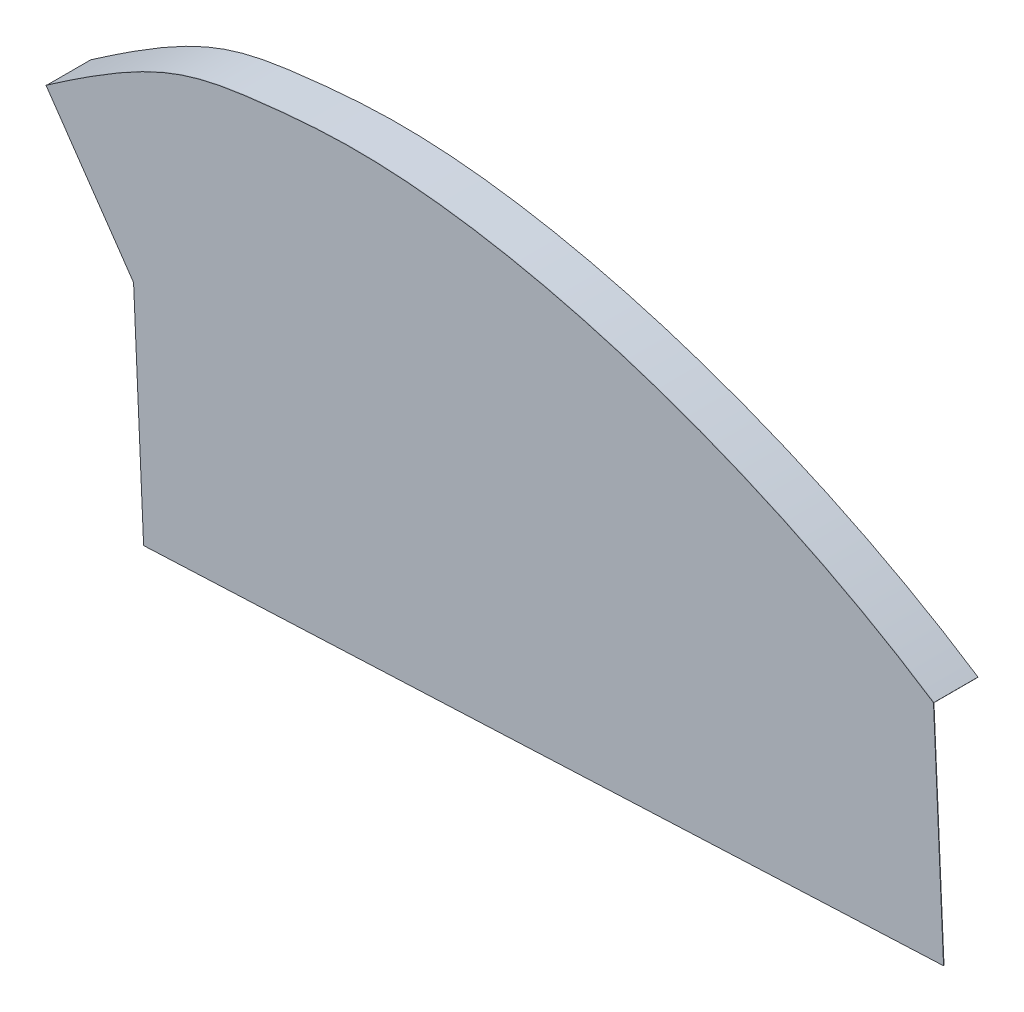
SolidWorks part; units mm, degrees
ref_plane "Front Plane" through (0, 0, 0) normal (0, 0, 1) x (1, 0, 0)
ref_plane "Top Plane" through (0, 0, 0) normal (0, 1, 0) x (1, 0, 0)
ref_plane "Right Plane" through (0, 0, 0) normal (1, 0, 0) x (0, 0, -1)
sketch "Sketch1" plane through (0, 0, 0) normal (0, 0, 1) x (1, 0, 0)
  line L0 (-169.0031, 11.7142) -> (-694.187, 895.1707) construction
  line L1 (-1544.65, 573.4414) -> (-1542.3973, 523.4922)
  line L2 (-1743.608, 593.8305) -> (-1723.9756, 565.3542)
  line L3 (-1544.65, 573.4414) -> (-1723.9756, 565.3542) construction
  line L4 (-1723.9756, 565.3542) -> (-1721.723, 515.405)
  line L5 (-1542.3973, 523.4922) -> (-1721.723, 515.405)
  spline S0 degree 3 poles (-1743.608, 593.8305) (-1719.5079, 610.5378) (-1709.3895, 613.3998) (-1646.2803, 619.2418) (-1585.7166, 600.4239) (-1544.65, 573.4414) knots 0 0 0 0 0.320555 0.420555 1 1 1 1
  point P6 (-1749.4095, 514.1564)
  point P7 (-864.9195, 554.0451)
  dimension "D1" = 200
extrude "Boss-Extrude1" add sketch "Sketch1" along normal blind 0.1
sketch "Sketch2" plane through (0, 0, 0.1) normal (0, 0, 1) x (1, 0, 0)
  line L0 (-1743.5795, 593.7894) -> (-1743.5225, 593.7072)
  line L1 (-1743.5225, 593.7072) -> (-1743.5258, 593.705)
  line L2 (-1544.6774, 573.3996) -> (-1544.7323, 573.3161)
  spline S0 degree 1 poles (-1544.7323, 573.3161) (-1743.5225, 593.7072) knots 0 0 1 1 construction
  spline S1 degree 3 poles (-1544.7323, 573.3161) (-1546.9519, 574.7745) (-1551.4313, 577.6136) (-1560.6294, 583.0453) (-1572.4709, 589.3269) (-1587.0699, 596.0193) (-1606.8127, 603.7551) (-1626.6209, 609.6253) (-1645.7855, 613.4616) (-1659.664, 615.2751) (-1672.8554, 616.0005) (-1683.1758, 615.6072) (-1690.7192, 614.94) (-1697.6194, 614.1843) (-1704.9414, 613.1758) (-1711.5371, 611.5206) (-1716.9507, 609.4963) (-1721.2263, 607.5471) (-1725.8618, 605.0871) (-1730.1444, 602.545) (-1733.8948, 600.1759) (-1736.8861, 598.2226) (-1739.5484, 596.4355) (-1741.7757, 594.9144) (-1742.9458, 594.107) (-1743.5225, 593.7072) knots 0 0 0 0 0.03125 0.0625 0.125 0.1875 0.25 0.375 0.4375 0.5 0.5625 0.625 0.65625 0.6875 0.75 0.8125 0.84375 0.875 0.90625 0.9375 0.953125 0.96875 0.984375 0.992188 1 1 1 1
  spline S2 degree 3 poles (-5441.7825, 66.9602) (-761.6919, -48.2927) (-1398.4186, 590.7885) (-1664.0556, 615.6153) (-1668.4586, 615.8535) (-1674.8505, 615.9246) (-1676.9471, 615.8989) (-1681.054, 615.7601) (-1685.0709, 615.538) (-1688.8415, 615.2069) (-1692.4557, 614.85) (-1694.1826, 614.66) (-1699.0922, 614.0849) (-1702.0267, 613.6789) (-1710.3915, 612.0761) (-1715.3828, 610.4946) (-1793.3484, 571.9174) (-2005.5606, 336.6136) (-5085.4885, -1602.8491) knots -3.114349 -3.114349 -3.114349 -3.114349 0.5 0.5 0.5625 0.5625 0.59375 0.59375 0.625 0.65625 0.65625 0.6875 0.6875 0.75 0.75 0.875 0.875 2.388524 2.388524 2.388524 2.388524 only from (-1544.6774, 573.3996) to (-1743.5795, 593.7894)
  spline S3 degree 3 poles (-1544.6774, 573.3996) (-1580.1063, 596.6779) (-1623.4173, 611.8172) (-1664.0556, 615.6153) (-1668.4586, 615.8535) (-1674.8505, 615.9246) (-1676.9471, 615.8989) (-1681.054, 615.7601) (-1685.0709, 615.538) (-1688.8415, 615.2069) (-1692.4557, 614.85) (-1694.1826, 614.66) (-1699.0922, 614.0849) (-1702.0267, 613.6789) (-1710.3915, 612.0761) (-1715.3828, 610.4946) (-1727.2785, 604.6086) (-1734.1826, 600.3037) (-1743.5795, 593.7894) knots 0 0 0 0 0.5 0.5 0.5625 0.5625 0.59375 0.59375 0.625 0.65625 0.65625 0.6875 0.6875 0.75 0.75 0.875 0.875 1 1 1 1
  dimension "D1" = 0.05
  dimension "D2" = 0.1
extrude "Boss-Extrude2" add sketch "Sketch2" against normal blind 10 contours L2 S3 L0 S1
